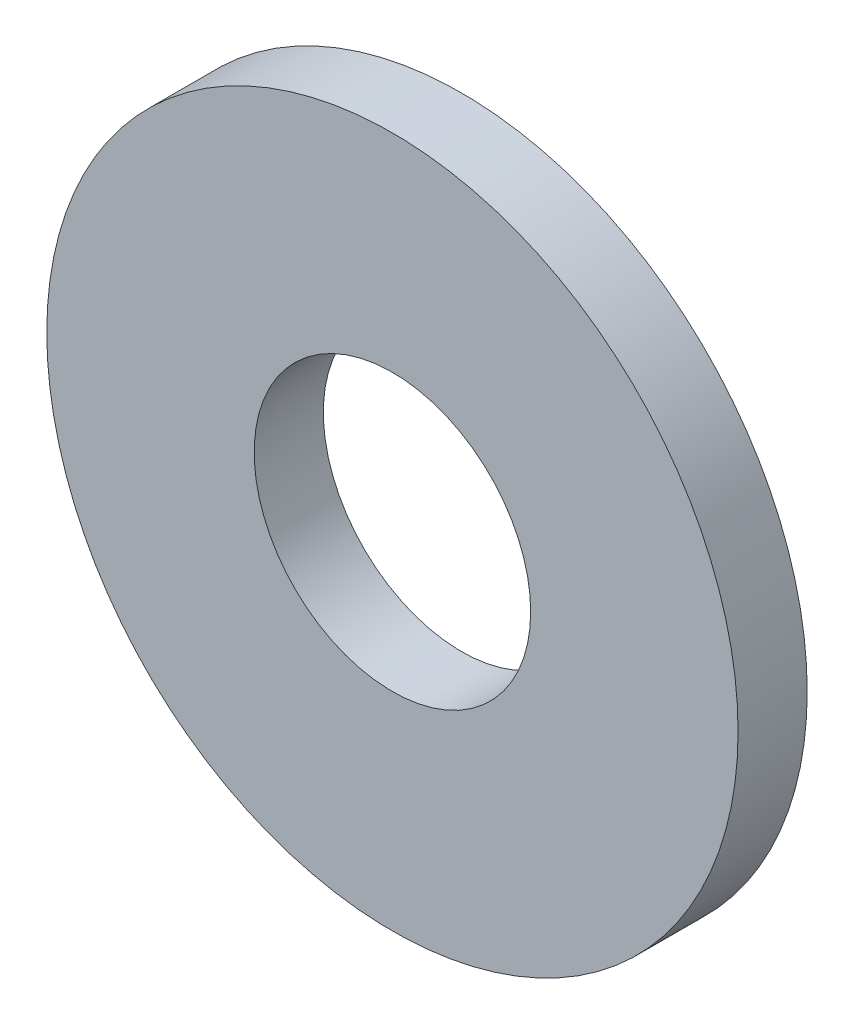
SolidWorks part; units mm, degrees
material "Aluminum Bronze"
ref_plane "Front Plane" through (0, 0, 0) normal (0, 0, 1) x (1, 0, 0)
ref_plane "Top Plane" through (0, 0, 0) normal (0, 1, 0) x (1, 0, 0)
ref_plane "Right Plane" through (0, 0, 0) normal (1, 0, 0) x (0, 0, -1)
sketch "Sketch1" plane through (0, 0, 0) normal (0, 0, 1) x (1, 0, 0)
  circle A0 centre (0, 0) radius 7.9375
  circle A1 centre (0, 0) radius 3.175
  dimension "D1" = 6.35
  dimension "D2" = 15.875
extrude "Boss-Extrude1" add sketch "Sketch1" along normal blind 1.5875
